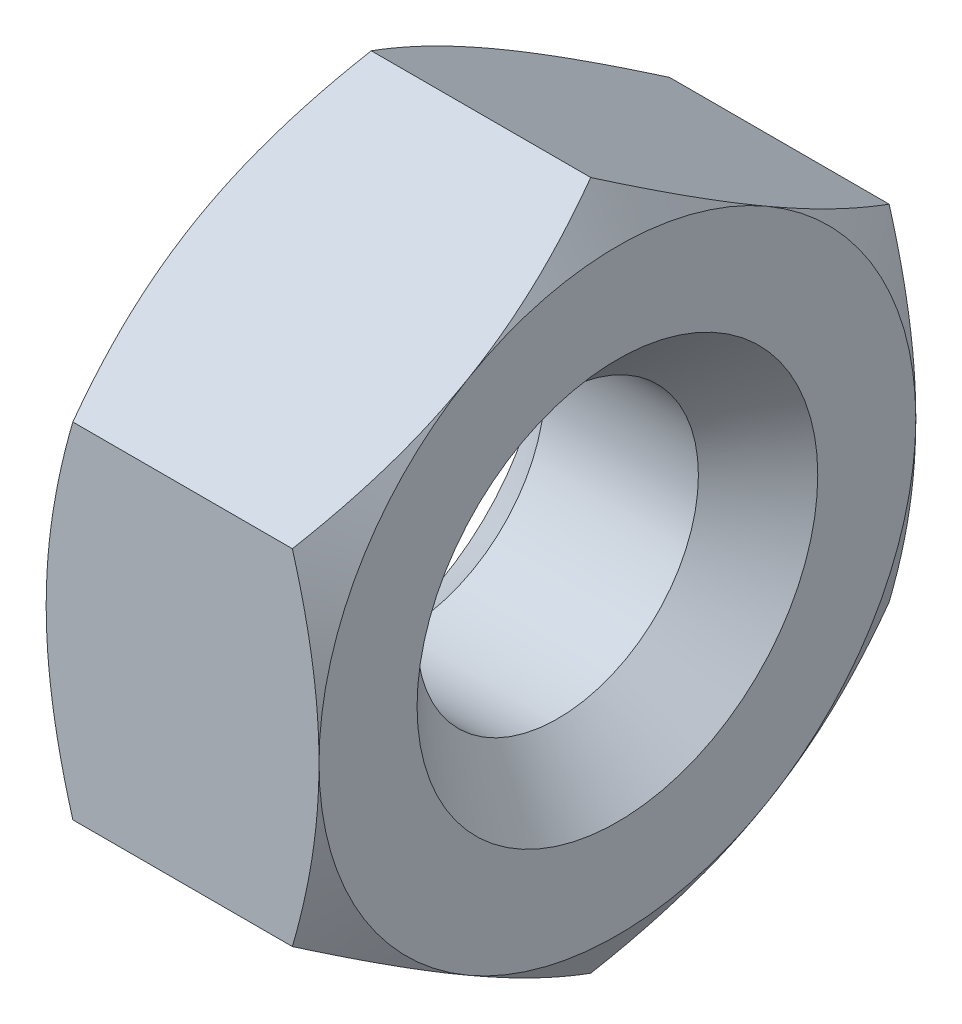
SolidWorks part; units mm, degrees
ref_plane "Front Plane" through (0, 0, 0) normal (0, 0, 1) x (1, 0, 0)
ref_plane "Top Plane" through (0, 0, 0) normal (0, 1, 0) x (1, 0, 0)
ref_plane "Right Plane" through (0, 0, 0) normal (1, 0, 0) x (0, 0, -1)
sketch "Sketch1" plane through (0, 0, 0) normal (1, 0, 0) x (0, 0, -1)
  line L0 (0, 0) -> (0, 10363.6103) construction
  line L1 (0, 0) -> (10363.6103, 0) construction
  line L3 (0, 4.0415) -> (-3.5, 2.0207)
  line L4 (-3.5, 2.0207) -> (-3.5, -2.0207)
  line L5 (-3.5, -2.0207) -> (0, -4.0415)
  line L6 (0, -4.0415) -> (3.5, -2.0207)
  line L7 (3.5, -2.0207) -> (3.5, 2.0207)
  line L8 (3.5, 2.0207) -> (0, 4.0415)
  circle A0 centre (0, 0) radius 3.5 construction
  dimension "S" = 7
extrude "m" add sketch "Sketch1" along normal mid plane 3.2
sketch "Sketch2" plane through (0, 0, 0) normal (0, 0, 1) x (1, 0, 0)
  line L0 (0, 0) -> (22.1176, 0) construction
  line L1 (1.6, 4.0415) -> (-1.6, 4.0415) construction
  line L2 (1.6, 4.0415) -> (1.2874, 4.0415)
  line L3 (1.6, 4.0415) -> (1.6, 2.0207) construction
  line L4 (1.6, 4.0415) -> (1.6, 3.5)
  line L5 (-1.6, 4.0415) -> (-1.6, 2.0207) construction
  line L6 (-1.6, 4.0415) -> (-1.6, 3.5)
  line L7 (-1.2874, 4.0415) -> (-1.6, 3.5)
  line L8 (1.2874, 4.0415) -> (1.6, 3.5)
  line L9 (-1.2874, 4.0415) -> (-1.6, 4.0415)
  dimension "D1" = 30
  dimension "D2" = 30
  dimension "ØD" = 7
revolve "Cut-Revolve1" cut sketch "Sketch2" angle 360 about L0
hole_wizard "d" positions "Sketch3" profile "Sketch4" tap size "M4" standard "ISO" end condition up to next
sketch "Sketch3" plane through (1.6, 0, 0) normal (1, 0, 0) x (0, 0, -1)
  point P0 (0, 0)
sketch "Sketch4" plane through (1.6, 0, 0) normal (0, 1, 0) x (0, 0, -1)
  line L0 (0, 0) -> (0, 3.2)
  line L1 (0, 3.2) -> (1.65, 3.2)
  line L2 (1.65, 3.2) -> (1.65, 0)
  line L5 (1.65, 0) -> (0, 0)
  line L11 (0, -6.35) -> (0, 107.95) construction
  dimension "Thru Tap Drill Dia." = 3.3
  dimension "Thru Tap Drill Depth" = 3.2
cosmetic thread "Hole Thread1" parameters "D2"=4
chamfer "Chamfer1" distance 0.7 angle 45 2 edges at (1.6, 0, -1.65) (-1.6, 0, -1.65)
